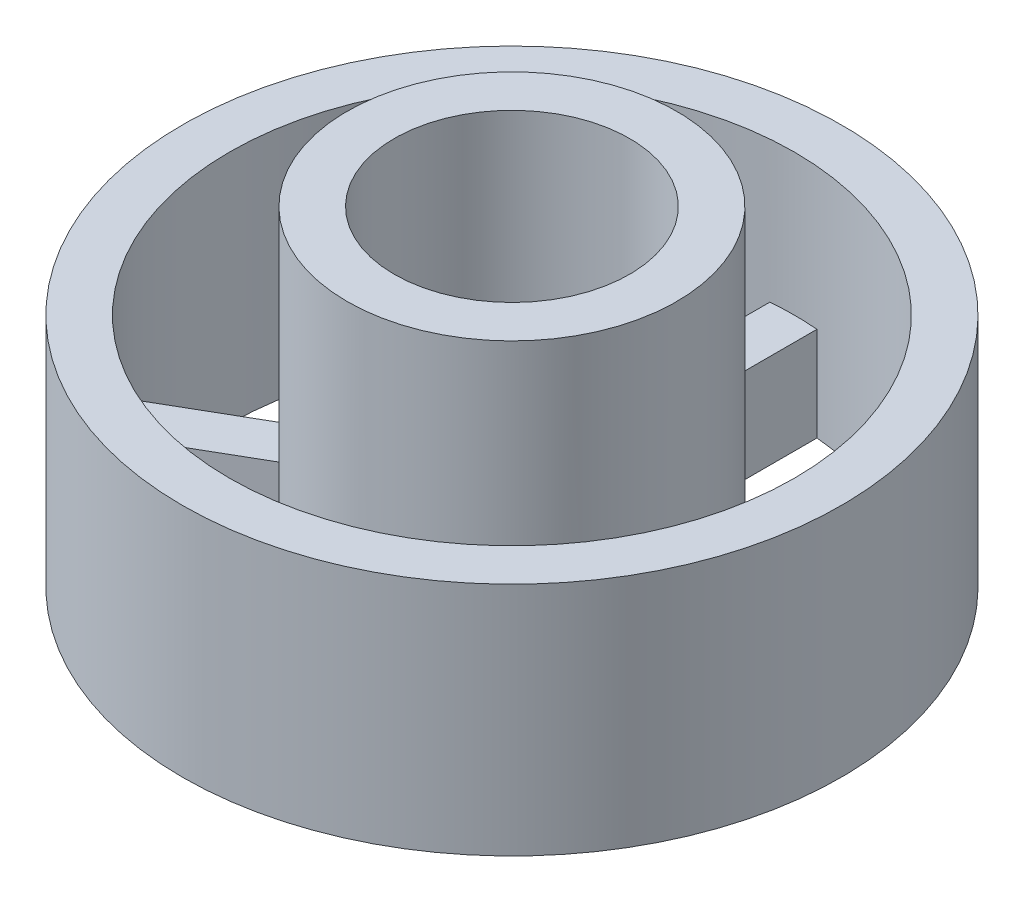
SolidWorks part; units mm, degrees
ref_plane "Front Plane" through (0, 0, 0) normal (0, 0, 1) x (1, 0, 0)
ref_plane "Top Plane" through (0, 0, 0) normal (0, 1, 0) x (1, 0, 0)
ref_plane "Right Plane" through (0, 0, 0) normal (1, 0, 0) x (0, 0, -1)
sketch "Sketch1" plane through (0, 0, 0) normal (0, 1, 0) x (1, 0, 0)
  circle A0 centre (0, 0) radius 7
  dimension "D1" = 14
extrude "Boss-Extrude1" add sketch "Sketch1" along normal blind 5 contours A0
sketch "Sketch2" plane through (0, 5, 0) normal (0, 1, 0) x (1, 0, 0)
  circle A0 centre (0, 0) radius 6
  dimension "D1" = 12
extrude "Cut-Extrude1" cut sketch "Sketch2" against normal blind 3
sketch "Sketch3" plane through (0, 2, 0) normal (0, 1, 0) x (1, 0, 0)
  circle A0 centre (0, 0) radius 3.5
  circle A1 centre (0, 0) radius 6 construction
  dimension "D1" = 2.5
extrude "Boss-Extrude3" add sketch "Sketch3" along normal blind 5
sketch "Sketch4" plane through (0, 7, 0) normal (0, 1, 0) x (1, 0, 0)
  circle A0 centre (0, 0) radius 2.5
  circle A1 centre (0, 0) radius 3.5 construction
  dimension "D1" = 1
extrude "Cut-Extrude2" cut sketch "Sketch4" against normal through all
sketch "Sketch5" plane through (0, 2, 0) normal (0, 1, 0) x (1, 0, 0)
  line L3 (-0.5, 5.9791) -> (-0.5, 3.4641)
  line L4 (0.5, 5.9791) -> (0.5, 3.4641)
  line L5 (-5.4281, -2.5566) -> (-3.25, -1.299)
  line L6 (-4.9281, -3.4226) -> (-2.75, -2.1651)
  line L7 (4.9281, -3.4226) -> (2.75, -2.1651)
  line L8 (5.4281, -2.5566) -> (3.25, -1.299)
  circle A0 centre (0, 0) radius 6 construction
  arc A1 (-0.5, 5.9791) -> (-5.4281, -2.5566) centre (0, 0) ccw
  arc A2 (-2.75, -2.1651) -> (2.75, -2.1651) centre (0, 0) ccw
  arc A3 (-4.9281, -3.4226) -> (4.9281, -3.4226) centre (0, 0) ccw
  arc A4 (3.25, -1.299) -> (0.5, 3.4641) centre (0, 0) ccw
  arc A5 (5.4281, -2.5566) -> (0.5, 5.9791) centre (0, 0) ccw
  arc A6 (-0.5, 3.4641) -> (-3.25, -1.299) centre (0, 0) ccw
  dimension "D5" = 1
  dimension "D7" = 1
extrude "Cut-Extrude3" cut sketch "Sketch5" against normal through all
